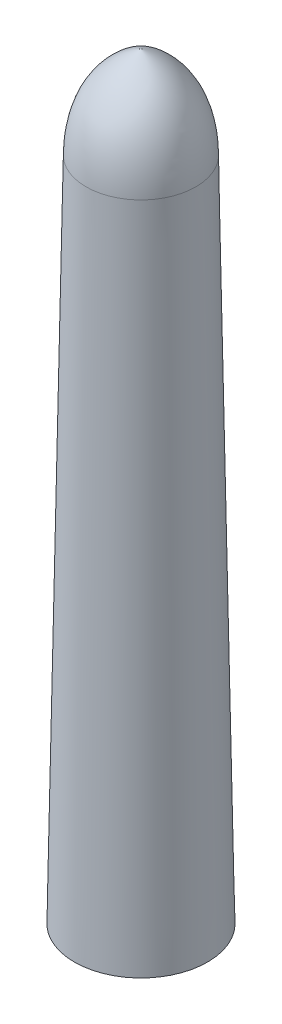
SolidWorks part; units mm, degrees
ref_plane "Front Plane" through (0, 0, 0) normal (0, 0, 1) x (1, 0, 0)
ref_plane "Top Plane" through (0, 0, 0) normal (0, 1, 0) x (1, 0, 0)
ref_plane "Right Plane" through (0, 0, 0) normal (1, 0, 0) x (0, 0, -1)
sketch "Sketch1" plane through (0, 0, 0) normal (0, 1, 0) x (1, 0, 0)
  circle A0 centre (0, 0) radius 20
  dimension "D1" = 40
extrude "Boss-Extrude1" add sketch "Sketch1" along normal blind 200 draft 1 contours A0
sketch "Sketch3" plane through (0, 0, 0) normal (0, -1, 0) x (1, 0, 0)
  circle A0 centre (0, 0) radius 18
  circle A1 centre (0, 0) radius 20
  circle A2 centre (0, 0) radius 20
  dimension "D1" = 0
extrude "Cut-Extrude1" cut sketch "Sketch3" against normal blind 200 draft 1 contours A0
sketch "Sketch4" plane through (0, 0, 0) normal (0, 0, 1) x (1, 0, 0)
  line L0 (0, 227.6608) -> (0, 225.6608)
  line L2 (16.509, 200) -> (-16.509, 200) construction
  line L3 (14.509, 200) -> (16.509, 200)
  line L4 (0, 220.6069) -> (0, 210.5526)
  spline S1 degree 2 poles (0, 227.6608) (16.1652, 220.5694) (16.509, 200) knots 0 0 0 1 1 1
  spline S2 degree 3 poles (0, 225.6608) (3.6622, 224.4293) (11.6244, 218.278) (14.3579, 208.6871) (14.509, 200) knots 0 0 0 0 0.332211 1 1 1 1
  dimension "D2" = 2
  dimension "D4" = 2
revolve "Revolve1" add sketch "Sketch4" angle 360 about L4
